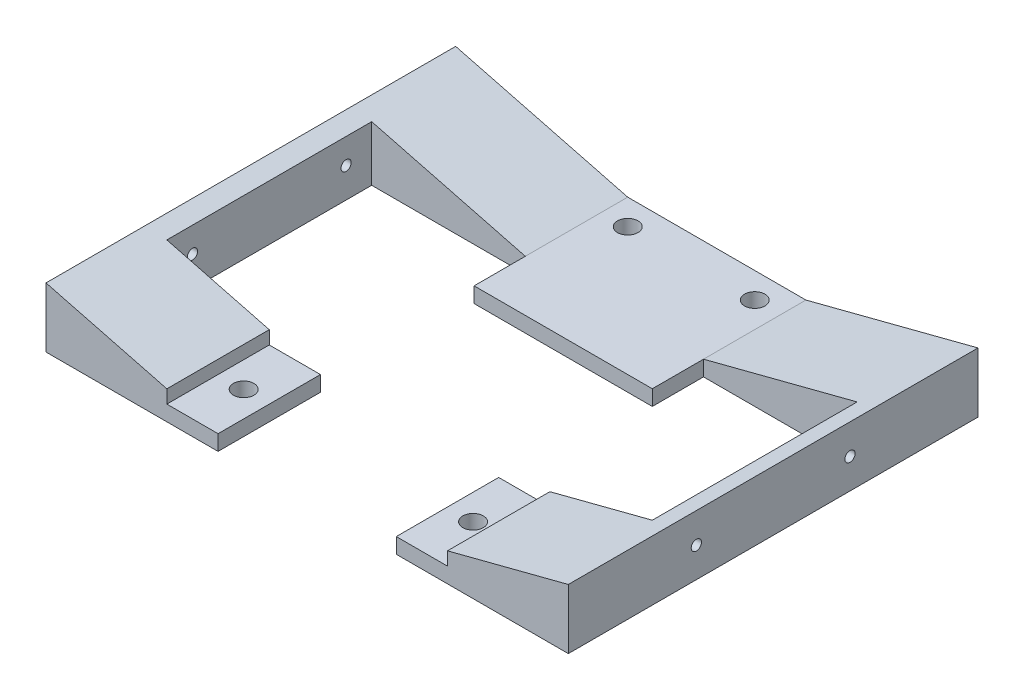
SolidWorks part; units mm, degrees
ref_plane "Front Plane" through (0, 0, 0) normal (0, 0, 1) x (1, 0, 0)
ref_plane "Top Plane" through (0, 0, 0) normal (0, 1, 0) x (1, 0, 0)
ref_plane "Right Plane" through (0, 0, 0) normal (1, 0, 0) x (0, 0, -1)
sketch "Sketch1" plane through (0, 0, 0) normal (0, 1, 0) x (1, 0, 0)
  line L1 (-129.54, 149.225) -> (129.54, 149.225)
  line L2 (-129.54, 149.225) -> (-129.54, -149.225)
  line L3 (-129.54, -149.225) -> (129.54, -149.225)
  line L4 (129.54, 149.225) -> (129.54, -149.225)
  point P4 (0, -149.225)
  point P6 (-129.54, 0)
  dimension "D1" = 298.45
  dimension "D2" = 259.08
extrude "Boss-Extrude3" add sketch "Sketch1" along normal blind 14.732
sketch "Sketch2" plane through (0, 0, 0) normal (0, -1, 0) x (1, 0, 0)
  line L1 (129.54, -149.225) -> (-129.54, -149.225)
  line L2 (129.54, -149.225) -> (129.54, 149.225)
  line L3 (129.54, 149.225) -> (-129.54, 149.225)
  line L4 (-129.54, -149.225) -> (-129.54, 149.225)
extrude "Boss-Extrude4" add sketch "Sketch2" along normal blind 22.098
sketch "Sketch4" plane through (129.54, 0, 0) normal (1, 0, 0) x (0, 0, -1)
  line L0 (0, -22.098) -> (-149.225, 0)
  line L2 (149.225, -22.098) -> (-149.225, -22.098) construction
  line L3 (142.494, 0) -> (-142.494, 0) construction
  line L5 (149.225, 14.732) -> (149.225, -22.098) construction
  line L6 (149.225, 0) -> (0, -22.098)
  line L8 (-149.225, 14.732) -> (149.225, 14.732)
  line L9 (-149.225, 14.732) -> (-149.225, 0)
  line L11 (149.225, 14.732) -> (149.225, 0)
  point P4 (0, 14.732)
  dimension "D1" = 298.45
  dimension "D2" = 14.732
extrude "Cut-Extrude2" cut sketch "Sketch4" against normal blind 259.08 flip side to cut
sketch "Sketch6" plane through (0, 0, 149.225) normal (0, 0, 1) x (1, 0, 0)
  line L0 (-44.196, -22.098) -> (44.196, -22.098)
  line L2 (-44.196, -22.098) -> (-129.54, 0)
  line L3 (-129.54, 14.732) -> (-129.54, 0) construction
  line L4 (142.494, 0) -> (-142.494, 0) construction
  line L6 (129.54, 14.732) -> (129.54, 0) construction
  line L7 (129.54, 0) -> (44.196, -22.098)
  line L9 (-129.54, 14.732) -> (129.54, 14.732)
  line L10 (-129.54, 14.732) -> (-129.54, 0)
  line L12 (129.54, 14.732) -> (129.54, 0)
  point P2 (0, -22.098)
  dimension "D1" = 88.392
  dimension "D2" = 36.83
extrude "Cut-Extrude4" cut sketch "Sketch6" against normal blind 298.45 flip side to cut
sketch "Sketch7" plane through (0, 0, 0) normal (0, 0, 1) x (1, 0, 0)
  line L3 (44.196, -27.178) -> (129.54, -5.08)
  line L4 (-44.196, -27.178) -> (44.196, -27.178)
  line L5 (-129.54, -5.08) -> (-44.196, -27.178)
  line L6 (-129.54, -5.08) -> (-129.54, -34.798)
  line L7 (-129.54, -34.798) -> (129.54, -34.798)
  line L8 (129.54, -34.798) -> (129.54, -5.08)
  dimension "D1" = 7.62
  dimension "D2" = 259.08
  dimension "D3" = 29.718
  dimension "D4" = 88.392
  dimension "D5" = 85.344
  dimension "D6" = 27.178
  dimension "D7" = 37.3886
extrude "Boss-Extrude6" add sketch "Sketch7" along normal blind 101.6 and the other way blind 101.6 separate body
sketch "Sketch8" plane through (0, 0, 101.6) normal (0, 0, 1) x (1, 0, 0)
  line L0 (-129.54, -34.798) -> (129.54, -34.798) construction
  line L1 (44.196, -27.178) -> (-44.196, -27.178) construction
  line L2 (-44.196, -34.798) -> (44.196, -34.798)
  line L3 (44.196, -27.178) -> (-44.196, -27.178)
  line L4 (-44.196, -27.178) -> (-44.196, -34.798)
  line L5 (44.196, -27.178) -> (44.196, -34.798)
extrude "Cut-Extrude5" cut sketch "Sketch8" against normal blind 127
delete or keep bodies "Body-Delete/Keep 2" type keep bodies bodies 110
sketch "Sketch10" plane through (0, 0, 0) normal (0, 0, 1) x (1, 0, 0)
  line L0 (-44.196, -27.178) -> (-129.54, -5.08) construction
  line L1 (129.54, -5.08) -> (44.196, -27.178) construction
  line L2 (-44.196, -27.178) -> (-120.396, -7.4476)
  line L3 (120.396, -7.4476) -> (44.196, -27.178)
  line L8 (120.396, -7.4476) -> (120.396, -34.798)
  line L9 (-129.54, -34.798) -> (129.54, -34.798) construction
  line L10 (120.396, -34.798) -> (44.196, -34.798)
  line L11 (44.196, -34.798) -> (44.196, -27.178)
  line L12 (-44.196, -27.178) -> (-44.196, -34.798)
  line L13 (-44.196, -34.798) -> (-120.396, -34.798)
  line L14 (-120.396, -34.798) -> (-120.396, -7.4476)
  dimension "D1" = 76.2
  dimension "D2" = 76.2
extrude "Cut-Extrude7" cut sketch "Sketch10" against normal blind 50.8 and the other way blind 50.8
sketch "Sketch13" plane through (-129.54, 0, 0) normal (-1, 0, 0) x (0, 0, 1)
  line L0 (-101.6, -5.08) -> (-101.6, -34.798)
  dimension "D1" = 29.718
sketch "Sketch15" plane through (0, 0, 101.6) normal (0, 0, 1) x (1, 0, 0)
  line L0 (129.54, -5.08) -> (44.196, -27.178) construction
  line L1 (44.196, -27.178) -> (69.596, -27.178)
  line L2 (44.196, -27.178) -> (44.196, -20.6012)
  line L3 (44.196, -20.6012) -> (69.596, -20.6012)
  line L4 (69.596, -27.178) -> (69.596, -20.6012)
  line L5 (44.196, -27.178) -> (69.596, -20.6012) construction
  line L6 (44.196, -20.6012) -> (69.596, -27.178) construction
  point P4 (56.896, -23.8896)
  dimension "D1" = 25.4
extrude "Cut-Extrude8" cut sketch "Sketch15" against normal blind 53.086
sketch "Sketch16" plane through (0, 0, 101.6) normal (0, 0, 1) x (1, 0, 0)
  line L0 (-44.196, -27.178) -> (-129.54, -5.08) construction
  line L1 (-44.196, -27.178) -> (-69.596, -27.178)
  line L2 (-44.196, -27.178) -> (-44.196, -20.6012)
  line L3 (-44.196, -20.6012) -> (-69.596, -20.6012)
  line L4 (-69.596, -27.178) -> (-69.596, -20.6012)
  line L5 (-44.196, -27.178) -> (-69.596, -20.6012) construction
  line L6 (-44.196, -20.6012) -> (-69.596, -27.178) construction
  point P4 (-56.896, -23.8896)
  dimension "D1" = 25.4
extrude "Cut-Extrude9" cut sketch "Sketch16" against normal blind 53.086
sketch "Sketch17" plane through (0, -27.178, 0) normal (0, 1, 0) x (1, 0, 0)
  line L0 (-44.196, 101.6) -> (-44.196, 50.8) construction
  line L1 (-44.196, 101.6) -> (-31.496, 101.6)
  line L2 (-44.196, 101.6) -> (-44.196, 88.9)
  line L3 (-44.196, 88.9) -> (-31.496, 88.9)
  line L4 (-31.496, 101.6) -> (-31.496, 88.9)
  line L5 (-44.196, 101.6) -> (-31.496, 88.9) construction
  line L6 (-44.196, 88.9) -> (-31.496, 101.6) construction
  line L7 (44.196, 101.6) -> (-44.196, 101.6) construction
  line L8 (0, 101.6) -> (0, 25.4) construction
  line L9 (44.196, 25.4) -> (-44.196, 25.4) construction
  line L10 (44.196, 101.6) -> (44.196, 88.9)
  line L11 (44.196, 101.6) -> (31.496, 101.6)
  line L12 (31.496, 101.6) -> (31.496, 88.9)
  line L13 (44.196, 88.9) -> (31.496, 88.9)
  circle A0 centre (-31.496, 88.9) radius 5.08
  circle A1 centre (31.496, 88.9) radius 5.08
  point P4 (-37.846, 95.25)
  dimension "D3" = 10.16
  dimension "D1" = 12.7
  dimension "D2" = 12.7
extrude "Cut-Extrude10" cut sketch "Sketch17" against normal through all contours A0 | A1
sketch "Sketch18" plane through (-129.54, 0, 0) normal (-1, 0, 0) x (0, 0, 1)
  line L0 (-101.6, -5.08) -> (101.6, -34.798) construction
  line L1 (101.6, -5.08) -> (-101.6, -34.798) construction
  line L3 (101.6, -19.939) -> (-101.6, -19.939) construction
  line L4 (101.6, -5.08) -> (101.6, -34.798) construction
  line L5 (-101.6, -5.08) -> (-101.6, -34.798) construction
  line L6 (0, -5.08) -> (0, -34.798) construction
  line L7 (-101.6, -5.08) -> (101.6, -5.08) construction
  line L8 (-101.6, -34.798) -> (101.6, -34.798) construction
  circle A0 centre (38.1, -19.939) radius 2.54
  circle A1 centre (-38.1, -19.939) radius 2.54
  dimension "D1" = 5.08
  dimension "D2" = 63.5
extrude "Cut-Extrude11" cut sketch "Sketch18" against normal through all
sketch "Sketch19" plane through (0, -27.178, 0) normal (0, 1, 0) x (1, 0, 0)
  line L0 (-56.896, -50.8) -> (-56.896, -101.6) construction
  line L1 (-44.196, -50.8) -> (-69.596, -50.8) construction
  line L2 (-69.596, -101.6) -> (-44.196, -101.6) construction
  line L3 (-69.596, -76.2) -> (-44.196, -76.2) construction
  line L4 (-69.596, -50.8) -> (-69.596, -101.6) construction
  line L5 (-44.196, -50.8) -> (-44.196, -101.6) construction
  circle A0 centre (-56.896, -76.2) radius 5.08
  dimension "D1" = 10.16
extrude "Cut-Extrude12" cut sketch "Sketch19" against normal through all
sketch "Sketch21" plane through (0, -27.178, 0) normal (0, 1, 0) x (1, 0, 0)
  line L0 (56.896, -50.8) -> (56.896, -101.6) construction
  line L1 (44.196, -50.8) -> (69.596, -50.8) construction
  line L2 (44.196, -101.6) -> (69.596, -101.6) construction
  line L3 (44.196, -76.2) -> (69.596, -76.2) construction
  line L4 (44.196, -50.8) -> (44.196, -101.6) construction
  line L5 (69.596, -50.8) -> (69.596, -101.6) construction
  circle A0 centre (56.896, -76.2) radius 5.08
  dimension "D1" = 10.16
extrude "Cut-Extrude13" cut sketch "Sketch21" against normal through all
